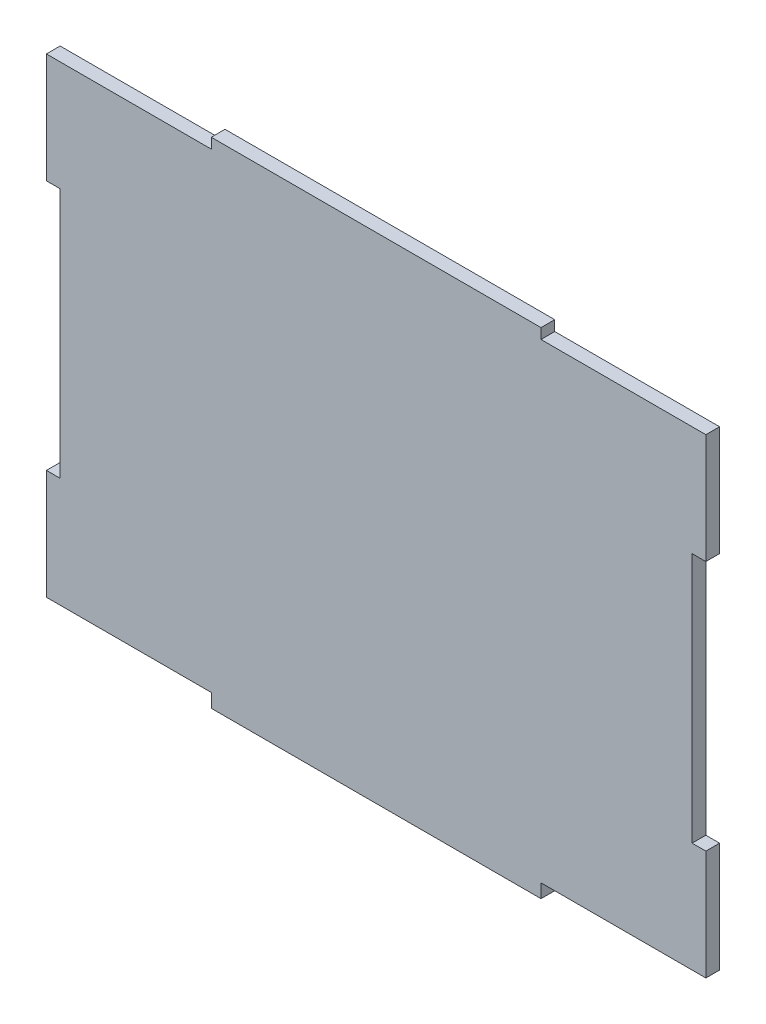
SolidWorks part; units mm, degrees
ref_plane "正面" through (0, 0, 0) normal (0, 0, 1) x (1, 0, 0)
ref_plane "平面" through (0, 0, 0) normal (0, 1, 0) x (1, 0, 0)
ref_plane "右側面" through (0, 0, 0) normal (1, 0, 0) x (0, 0, -1)
sketch "ｽｹｯﾁ1" plane through (0, 0, 0) normal (0, 0, 1) x (1, 0, 0)
  line L1 (-45.9728, 49.5738) -> (50.0272, 49.5738)
  line L2 (-45.9728, 49.5738) -> (-45.9728, -22.4262)
  line L3 (-45.9728, -22.4262) -> (50.0272, -22.4262)
  line L4 (50.0272, 49.5738) -> (50.0272, -22.4262)
  dimension "D1" = 96
  dimension "D2" = 72
extrude "ﾎﾞｽ - 押し出し1" add sketch "ｽｹｯﾁ1" along normal blind 2
sketch "ｽｹｯﾁ2" plane through (0, 0, 0) normal (0, 0, -1) x (-1, 0, 0)
  line L0 (-50.0272, -20.4262) -> (-26.0272, -20.4262) construction
  line L1 (45.9728, -22.4262) -> (21.9728, -22.4262)
  line L2 (45.9728, -22.4262) -> (45.9728, -20.4262)
  line L3 (45.9728, -20.4262) -> (21.9728, -20.4262)
  line L4 (21.9728, -22.4262) -> (21.9728, -20.4262)
  line L5 (-50.0272, 48.0738) -> (-26.0272, 48.0738) construction
  line L6 (-50.0272, -22.4262) -> (-26.0272, -22.4262)
  line L7 (-50.0272, -22.4262) -> (-50.0272, -20.4262)
  line L8 (-50.0272, -20.4262) -> (-26.0272, -20.4262)
  line L9 (-26.0272, -22.4262) -> (-26.0272, -20.4262)
  line L10 (45.9728, 50.0738) -> (21.9728, 50.0738)
  line L11 (45.9728, 50.0738) -> (45.9728, 48.0738)
  line L12 (45.9728, 48.0738) -> (21.9728, 48.0738)
  line L13 (21.9728, 50.0738) -> (21.9728, 48.0738)
  line L15 (-50.0272, 50.0738) -> (-26.0272, 50.0738)
  line L16 (-50.0272, 50.0738) -> (-50.0272, 48.0738)
  line L17 (-50.0272, 48.0738) -> (-26.0272, 48.0738)
  line L18 (-26.0272, 50.0738) -> (-26.0272, 48.0738)
  dimension "D1" = 24
  dimension "D2" = 24
  dimension "D3" = 24
  dimension "D4" = 24
extrude "ｶｯﾄ - 押し出し1" cut sketch "ｽｹｯﾁ2" against normal through all
sketch "ｽｹｯﾁ3" plane through (0, 0, 0) normal (0, 0, -1) x (-1, 0, 0)
  line L1 (45.9728, -4.4262) -> (43.9728, -4.4262)
  line L2 (45.9728, -4.4262) -> (45.9728, 32.0738)
  line L3 (45.9728, 32.0738) -> (43.9728, 32.0738)
  line L4 (43.9728, -4.4262) -> (43.9728, 32.0738)
extrude "ｶｯﾄ - 押し出し2" cut sketch "ｽｹｯﾁ3" against normal through all
sketch "ｽｹｯﾁ4" plane through (0, 0, 0) normal (0, 0, -1) x (-1, 0, 0)
  line L1 (-50.0272, -4.4262) -> (-48.0272, -4.4262)
  line L2 (-50.0272, -4.4262) -> (-50.0272, 32.0738)
  line L3 (-50.0272, 32.0738) -> (-48.0272, 32.0738)
  line L4 (-48.0272, -4.4262) -> (-48.0272, 32.0738)
extrude "ｶｯﾄ - 押し出し3" cut sketch "ｽｹｯﾁ4" against normal through all
